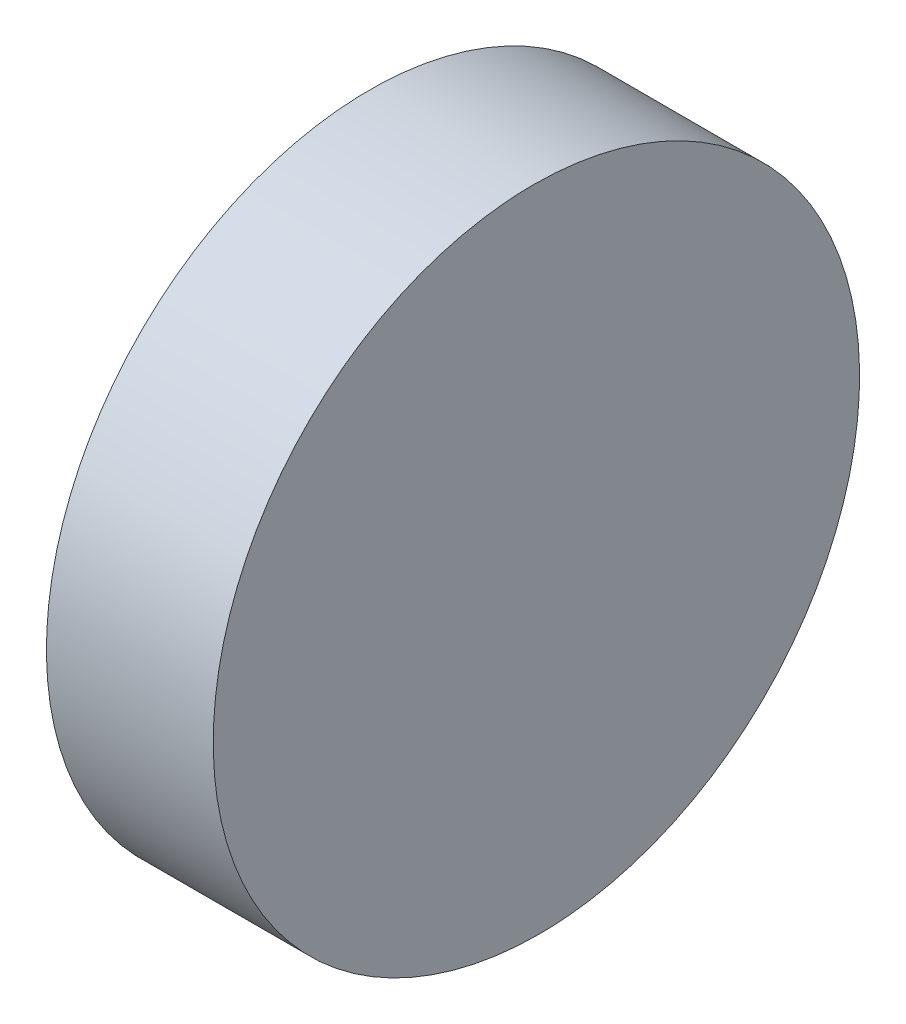
SolidWorks part; units mm, degrees
ref_plane "前视基准面" through (0, 0, 0) normal (0, 0, 1) x (1, 0, 0)
ref_plane "上视基准面" through (0, 0, 0) normal (0, 1, 0) x (1, 0, 0)
ref_plane "右视基准面" through (0, 0, 0) normal (1, 0, 0) x (0, 0, -1)
sketch "草图1" plane through (0, 0, 0) normal (0, 0, 1) x (1, 0, 0)
  line L0 (15.2768, 0) -> (-15.2768, 0) construction
  line L1 (0, 19.05) -> (0, -19.05)
  line L2 (0, -19.05) -> (10, -19.05)
  line L3 (10, -19.05) -> (9.6675, 19.05)
  line L4 (0, 19.05) -> (9.6675, 19.05)
  point P5 (0, 0)
  dimension "D1" = 10
  dimension "D2" = 38.1
  dimension "D3" = 0.5
extrude "凸台-拉伸1" add sketch "草图1" along normal blind 38.1 contours L1 L2 L3 L4
sketch "草图2" plane through (0, 0, 0) normal (-1, 0, 0) x (0, 0, 1)
  line L4 (0, 19.05) -> (0, -19.05)
  line L5 (0, -19.05) -> (38.1, -19.05)
  line L6 (38.1, -19.05) -> (38.1, 19.05)
  line L7 (38.1, 19.05) -> (0, 19.05)
  line L8 (0, 19.05) -> (0, -19.05)
  line L9 (0, -19.05) -> (38.1, -19.05)
  line L10 (38.1, -19.05) -> (38.1, 19.05)
  line L11 (38.1, 19.05) -> (0, 19.05)
  circle A0 centre (19.05, 0) radius 19.05
  point P7 (19.05, 19.05)
  line M1 (0, 19.05) -> (0, -19.05)
  line M2 (0, -19.05) -> (38.1, -19.05)
  line M3 (38.1, -19.05) -> (38.1, 19.05)
  line M4 (38.1, 19.05) -> (0, 19.05)
  dimension "D2" = 38.1
  dimension "D1" = 0
extrude "切除-拉伸1" cut sketch "草图2" against normal blind 10 contours A0 L8 M2 | A0 L9 M3 | A0 L10 M4 | A0 L11 M1
